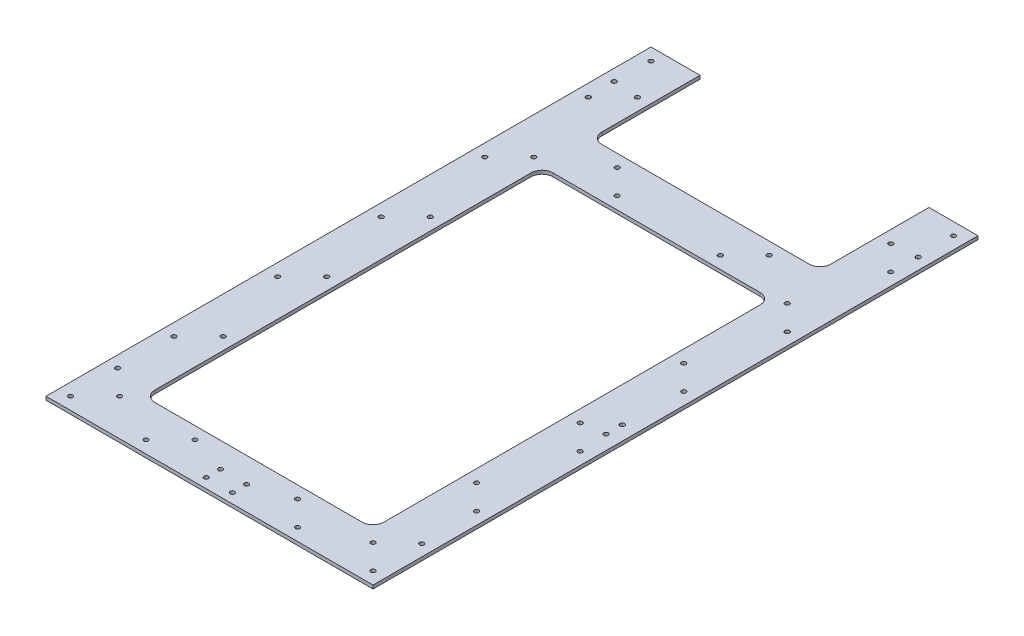
SolidWorks part; units mm, degrees
ref_plane "Front Plane" through (0, 0, 0) normal (0, 0, 1) x (1, 0, 0)
ref_plane "Top Plane" through (0, 0, 0) normal (0, 1, 0) x (1, 0, 0)
ref_plane "Right Plane" through (0, 0, 0) normal (1, 0, 0) x (0, 0, -1)
sketch "Sketch1" plane through (0, 0, 0) normal (0, 1, 0) x (1, 0, 0)
  line L1 (150, -300) -> (-150, -300)
  line L2 (150, -300) -> (150, 300)
  line L3 (150, 300) -> (-150, 300)
  line L4 (-150, -300) -> (-150, 300)
  line L5 (150, -300) -> (-150, 300) construction
  line L6 (150, 300) -> (-150, -300) construction
  point P0 (0, 0)
  dimension "D1" = 600
  dimension "D2" = 300
extrude "Boss-Extrude1" add sketch "Sketch1" along normal blind 3.175
sketch "Sketch3" plane through (0, 3.175, 0) normal (0, 1, 0) x (1, 0, 0)
  line L0 (-95, -255) -> (95, -255)
  line L1 (0, 255) -> (0, -300) construction
  line L2 (105, -245) -> (105, 100)
  line L3 (95, 110) -> (-95, 110)
  line L4 (105, 255) -> (105, 165)
  line L5 (150, 300) -> (-150, 300) construction
  line L6 (95, 155) -> (-95, 155)
  line L8 (0, -300) -> (0, -342.0806) construction
  line L9 (-105, 255) -> (-105, 165)
  line L10 (-105, -245) -> (-105, 100)
  line L11 (50.6601, -255) -> (50.6601, -300) construction
  line L12 (-150, -300) -> (150, -300) construction
  line L13 (105, 27.7939) -> (150, 27.7939) construction
  line L14 (150, -300) -> (150, 300) construction
  line L15 (-150, 27.7939) -> (-105, 27.7939) construction
  line L16 (-150, 300) -> (-150, -300) construction
  line L17 (54.6047, 155) -> (54.6047, 110) construction
  line L18 (105, 255) -> (150, 255)
  line L19 (150, 255) -> (150, 300)
  line L20 (150, 300) -> (-150, 300)
  line L21 (-150, 300) -> (-150, 255)
  line L22 (-150, 255) -> (-105, 255)
  arc A1 (-105, 165) -> (-95, 155) centre (-95, 165) ccw
  arc A3 (105, 165) -> (95, 155) centre (95, 165) cw
  arc A4 (105, 100) -> (95, 110) centre (95, 100) ccw
  arc A5 (-105, 100) -> (-95, 110) centre (-95, 100) cw
  arc A6 (-105, -245) -> (-95, -255) centre (-95, -245) ccw
  arc A7 (95, -255) -> (105, -245) centre (95, -245) ccw
  point P17 (0, 300)
  point P18 (0, 155)
  point P19 (0, 110)
  point P20 (0, -255)
  point P22 (-105.4457, 300)
  point P25 (-105, 155)
  point P28 (105.4457, 300)
  point P31 (105, 155)
  point P34 (105, 110)
  point P37 (-105, 110)
  point P40 (-105, -255)
  point P43 (105, -255)
  dimension "D1" = 45
  dimension "D4" = 10
  dimension "D2" = 45
  dimension "D3" = 145
extrude "Cut-Extrude1" cut sketch "Sketch3" against normal blind 10
sketch "Sketch4" plane through (0, 3.175, 0) normal (0, 1, 0) x (1, 0, 0)
  line L0 (-150, -300) -> (150, -300) construction
  circle A0 centre (12, -291) radius 2.05
  circle A1 centre (-12, -291) radius 2.05
  circle A2 centre (-12, -278) radius 2.05
  circle A3 centre (12, -278) radius 2.05
  point P16 (-27, -300)
  dimension "D1" = 4.1
  dimension "D2" = 15
  dimension "D3" = 39
  dimension "D4" = 9
  dimension "D5" = 22
extrude "Cut-Extrude2" cut sketch "Sketch4" against normal blind 51
sketch "Sketch5" plane through (0, 3.175, 0) normal (0, 1, 0) x (1, 0, 0)
  line L0 (150, -300) -> (150, 255) construction
  circle A0 centre (137, -73.2648) radius 2.1
  circle A1 centre (137, -58.2648) radius 2.1
  dimension "D1" = 4.2
  dimension "D2" = 13
extrude "Cut-Extrude3" cut sketch "Sketch5" against normal blind 67
sketch "Sketch7" plane through (0, 3.175, 0) normal (0, 1, 0) x (1, 0, 0)
  line L0 (138.75, -300) -> (138.75, 255) construction
  line L1 (116.25, -300) -> (116.25, 255) construction
  line L2 (150, -187.519) -> (138.75, -187.519) construction
  line L3 (150, -300) -> (150, 255) construction
  line L4 (138.75, -187.519) -> (127.5, -187.519) construction
  line L5 (127.5, -187.519) -> (116.25, -187.519) construction
  line L6 (116.25, -187.519) -> (105, -187.519) construction
  line L7 (105, -245) -> (105, 100) construction
  line L8 (-150, -300) -> (150, -300) construction
  line L10 (150, 121.25) -> (0, 121.25) construction
  line L11 (105, 255) -> (150, 255) construction
  line L12 (150, 143.75) -> (0, 143.75) construction
  line L13 (33.148, 155) -> (33.148, 143.75) construction
  line L14 (-95, 155) -> (95, 155) construction
  line L15 (33.148, 143.75) -> (33.148, 132.5) construction
  line L16 (33.148, 132.5) -> (33.148, 121.25) construction
  line L17 (33.148, 121.25) -> (33.148, 110) construction
  line L18 (95, 110) -> (-95, 110) construction
  line L19 (150, -288.75) -> (0, -288.75) construction
  line L20 (150, -266.25) -> (0, -266.25) construction
  line L21 (55.7313, -255) -> (55.7313, -266.25) construction
  line L22 (-95, -255) -> (95, -255) construction
  line L23 (55.7313, -266.25) -> (55.7313, -277.5) construction
  line L24 (55.7313, -277.5) -> (55.7313, -288.75) construction
  line L25 (55.7313, -288.75) -> (55.7313, -300) construction
  line L26 (-42.5408, 110) -> (-42.5408, -255) construction
  line L27 (0, -288.75) -> (0, -389.9124) construction
  line L29 (-150, 255) -> (-105, 255) construction
  circle A0 centre (138.75, -288.75) radius 2.05
  circle A1 centre (116.25, -266.25) radius 2.05
  circle A2 centre (47.0236, -266.25) radius 2.05
  circle A3 centre (69.5236, -288.75) radius 2.05
  circle A4 centre (116.25, -171.25) radius 2.05
  circle A5 centre (138.75, -193.75) radius 2.05
  circle A6 centre (116.25, -76.25) radius 2.05
  circle A7 centre (138.75, -98.75) radius 2.05
  circle A8 centre (116.25, 18.75) radius 2.05
  circle A9 centre (138.75, -3.75) radius 2.05
  circle A10 centre (116.25, 113.75) radius 2.05
  circle A11 centre (138.75, 91.25) radius 2.05
  circle A12 centre (116.25, 208.75) radius 2.05
  circle A13 centre (138.75, 186.25) radius 2.05
  circle A16 centre (47.3578, 121.25) radius 2.05
  circle A17 centre (69.635, 143.75) radius 2.05
  circle A18 centre (-47.3578, 121.25) radius 2.05
  circle A19 centre (-69.635, 143.75) radius 2.05
  circle A21 centre (-116.25, 208.75) radius 2.05
  circle A22 centre (-138.75, 186.25) radius 2.05
  circle A23 centre (-138.75, 91.25) radius 2.05
  circle A24 centre (-116.25, 18.75) radius 2.05
  circle A25 centre (-116.25, 113.75) radius 2.05
  circle A26 centre (-116.25, -76.25) radius 2.05
  circle A27 centre (-138.75, -3.75) radius 2.05
  circle A28 centre (-138.75, -98.75) radius 2.05
  circle A29 centre (-116.25, -171.25) radius 2.05
  circle A30 centre (-138.75, -193.75) radius 2.05
  circle A31 centre (-116.25, -266.25) radius 2.05
  circle A32 centre (-138.75, -288.75) radius 2.05
  circle A33 centre (-47.0236, -266.25) radius 2.05
  circle A34 centre (-69.5236, -288.75) radius 2.05
  circle A35 centre (116.25, 303.75) radius 2.05 [skipped]
  circle A36 centre (138.75, 281.25) radius 2.05 [skipped]
  circle A37 centre (-138.75, 243.75) radius 2.05
  circle A38 centre (138.75, 243.75) radius 2.05
  dimension "D1" = 4.1
  dimension "D2" = 4.1
  dimension "D6" = 4.1
  dimension "D5" = 95
  dimension "D7" = 11.25
  dimension "D3" = 2
  dimension "D4" = 7
extrude "Cut-Extrude4" cut sketch "Sketch7" against normal blind 10
sketch "Sketch8" plane through (0, 3.175, 0) normal (0, 1, 0) x (1, 0, 0)
  line L0 (150, -300) -> (150, 255) construction
  circle A0 centre (139.5, 210.666) radius 2.1
  circle A1 centre (139.5, -244.7019) radius 2.1
  dimension "D1" = 4.2
  dimension "D2" = 10.5
extrude "Cut-Extrude5" cut sketch "Sketch8" against normal blind 10
ref_plane "Plane1" through (0, 0, 0) normal (1, 0, 0) x (0, 0, -1)
mirror "Mirror1" about plane through (0, 0, 0) normal (1, 0, 0) of "Cut-Extrude5"
equation "\"D2@Sketch7\"=\"D1@Sketch7\""
